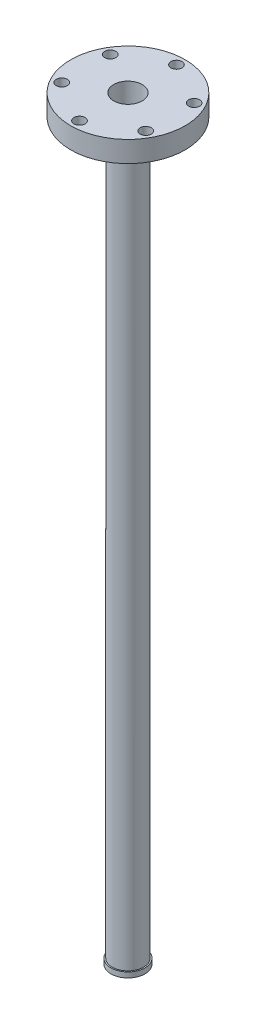
SolidWorks part; units mm, degrees
ref_plane "Front Plane" through (0, 0, 0) normal (0, 0, 1) x (1, 0, 0)
ref_plane "Top Plane" through (0, 0, 0) normal (0, 1, 0) x (1, 0, 0)
ref_plane "Right Plane" through (0, 0, 0) normal (1, 0, 0) x (0, 0, -1)
sketch "Sketch1" plane through (0, 0, 0) normal (0, 1, 0) x (1, 0, 0)
  circle A0 centre (0, 0) radius 9.525
  circle A1 centre (0, 0) radius 8.636
  dimension "D1" = 19.05
  dimension "D2" = 17.272
extrude "Extrude1" add sketch "Sketch1" along normal blind 457.2
sketch "Sketch2" plane through (0, 457.2, 0) normal (0, 1, 0) x (1, 0, 0)
  circle A0 centre (0, 0) radius 8.636
  circle A1 centre (0, 0) radius 34.671
  dimension "D1" = 69.342
extrude "Extrude2" add sketch "Sketch2" against normal blind 12.7
sketch "Sketch3" plane through (0, 457.2, 0) normal (0, 1, 0) x (1, 0, 0)
  line L0 (0, 0) -> (0, 29.3624) construction
  circle A0 centre (0, 29.3624) radius 3.3655
  dimension "D1" = 6.731
  dimension "D2" = 29.3624
extrude "Extrude3" cut sketch "Sketch3" against normal through all
pattern_circular "CirPattern1" count 6 over 360 about axis through (0, 0, 0) along (0, 1, 0) of "Extrude3"
sketch "Sketch4" plane through (0, 0, 0) normal (0, -1, 0) x (1, 0, 0)
  circle A0 centre (0, 0) radius 8.636
  circle A1 centre (0, 0) radius 10.3187
  dimension "D1" = 20.6375
extrude "Extrude4" add sketch "Sketch4" against normal blind 3.175
